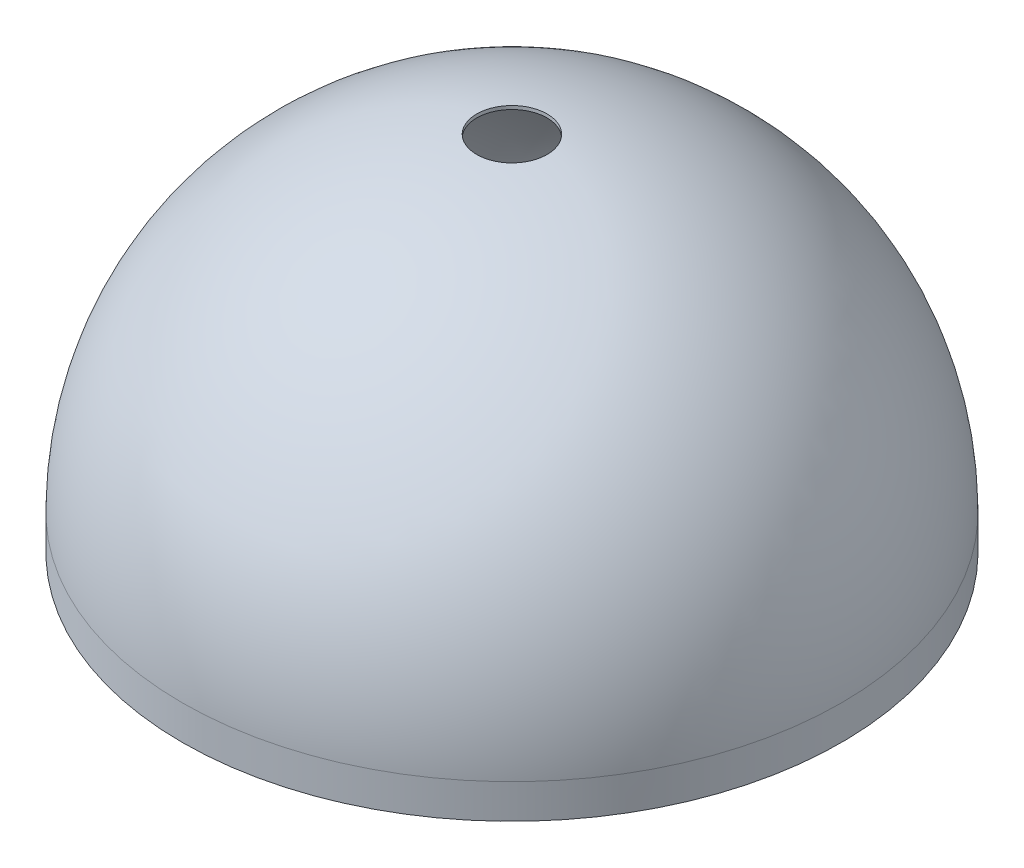
SolidWorks part; units mm, degrees
ref_plane "Front Plane" through (0, 0, 0) normal (0, 0, 1) x (1, 0, 0)
ref_plane "Top Plane" through (0, 0, 0) normal (0, 1, 0) x (1, 0, 0)
ref_plane "Right Plane" through (0, 0, 0) normal (1, 0, 0) x (0, 0, -1)
sketch "Sketch2" plane through (0, 0, 0) normal (1, 0, 0) x (0, 0, -1)
  line L0 (0, 0) -> (0, 24.13)
  line L1 (0, 0) -> (24.13, 0)
  line L2 (24.13, 0) -> (24.384, 0)
  line L3 (0, 24.13) -> (0, 24.384)
  line L4 (0, 0) -> (0, 26.9464) construction
  arc A0 (24.13, 0) -> (0, 24.13) centre (0, 0) ccw
  arc A3 (24.384, 0) -> (0, 24.384) centre (0, 0) ccw
  arc A4 (24.13, 0) -> (0, 24.13) centre (0, 0) ccw
  dimension "D1" = 48.26
  dimension "D2" = 48.768
revolve "Revolve1" add sketch "Sketch2" angle 360 about L4
sketch "Sketch3" plane through (0, 0, 0) normal (0, 1, 0) x (1, 0, 0)
  circle A0 centre (0, 0) radius 2.6035
  dimension "D1" = 5.207
extrude "Cut-Extrude1" cut sketch "Sketch3" along normal through all
sketch "Sketch4" plane through (0, 0, 0) normal (0, 1, 0) x (1, 0, 0)
  circle A0 centre (0, 0) radius 24.384
  circle A1 centre (0, 0) radius 24.13
  dimension "D1" = 48.768
  dimension "D2" = 48.26
extrude "Boss-Extrude1" add sketch "Sketch4" against normal blind 2.54
